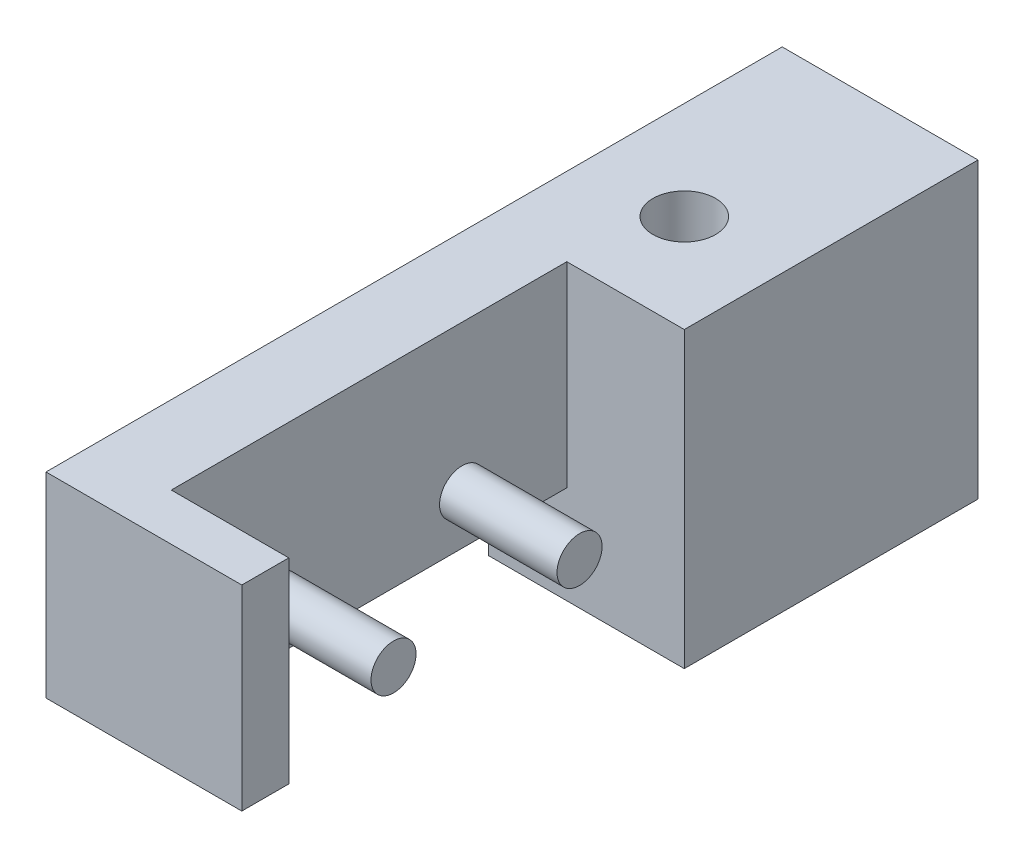
SolidWorks part; units mm, degrees
ref_plane "前视基准面" through (0, 0, 0) normal (0, 0, 1) x (1, 0, 0)
ref_plane "上视基准面" through (0, 0, 0) normal (0, 1, 0) x (1, 0, 0)
ref_plane "右视基准面" through (0, 0, 0) normal (1, 0, 0) x (0, 0, -1)
sketch "草图1" plane through (0, 0, 0) normal (1, 0, 0) x (0, 0, -1)
  line L0 (0, 0) -> (15, 0)
  line L1 (15, 0) -> (15, 15)
  line L2 (15, 15) -> (-22.6, 15)
  line L3 (-22.6, 15) -> (-22.6, 5)
  line L4 (-22.6, 5) -> (0, 5)
  line L5 (0, 5) -> (0, 4)
  line L7 (0, 4) -> (0, 0)
  point P3 (0, 0)
  dimension "D1" = 5
  dimension "D2" = 15
  dimension "D4" = 22.6
  dimension "D5" = 10
extrude "凸台-拉伸1" add sketch "草图1" along normal mid plane 10
sketch "草图2" plane through (5, 0, 0) normal (1, 0, 0) x (0, 0, -1)
  line L0 (-22.6, 5) -> (0, 5) construction
  line L1 (-20.2, 5) -> (0, 5)
  line L2 (-20.2, 5) -> (-20.2, 15)
  line L3 (-20.2, 15) -> (0, 15)
  line L4 (0, 5) -> (0, 15)
  line L5 (-22.6, 15) -> (-22.6, 5) construction
  dimension "D1" = 10
  dimension "D2" = 2.4
  dimension "D3" = 20.2
extrude "切除-拉伸1" cut sketch "草图2" against normal blind 6
sketch "草图3" plane through (-1, 0, 0) normal (1, 0, 0) x (0, 0, -1)
  line L0 (-14.85, 7.5) -> (-5.35, 7.5) construction
  line L1 (-10.1, 7.5) -> (-10.1, 5) construction
  line L3 (-20.2, 5) -> (0, 5) construction
  circle A0 centre (-14.85, 7.5) radius 1.15
  circle A1 centre (-5.35, 7.5) radius 1.15
  dimension "D1" = 2.3
  dimension "D2" = 2.3
  dimension "D3" = 9.5
  dimension "D4" = 2.5
extrude "凸台-拉伸2" add sketch "草图3" along normal blind 6
sketch "草图5" plane through (0, 0, 0) normal (0, -1, 0) x (1, 0, 0)
  line L0 (5, 0) -> (-5, 0) construction
  circle A0 centre (0, -5) radius 1.6
  dimension "D1" = 3.2
  dimension "D2" = 5
extrude "切除-拉伸2" cut sketch "草图5" against normal up to next
